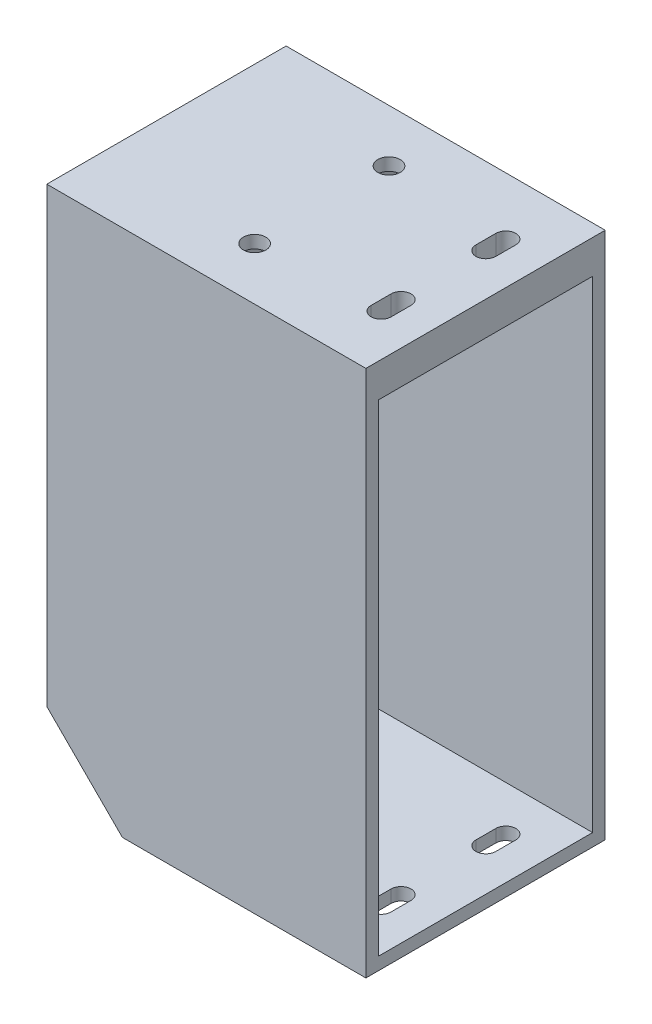
SolidWorks part; units mm, degrees
ref_plane "Front Plane" through (0, 0, 0) normal (0, 0, 1) x (1, 0, 0)
ref_plane "Top Plane" through (0, 0, 0) normal (0, 1, 0) x (1, 0, 0)
ref_plane "Right Plane" through (0, 0, 0) normal (1, 0, 0) x (0, 0, -1)
sketch "Sketch2" plane through (0, 0, 0) normal (1, 0, 0) x (0, 0, -1)
  line L0 (-22.6038, 17.8808) -> (-22.6038, -96.8692)
  line L1 (-22.6038, -96.8692) -> (28.3962, -96.8692)
  line L2 (28.3962, -96.8692) -> (28.3962, 17.8808)
  line L3 (28.3962, 17.8808) -> (-22.6038, 17.8808)
  line L4 (-25.6038, 20.8808) -> (-25.6038, -99.8692)
  line L5 (-25.6038, -99.8692) -> (31.3962, -99.8692)
  line L6 (31.3962, -99.8692) -> (31.3962, 20.8808)
  line L7 (31.3962, 20.8808) -> (-25.6038, 20.8808)
  dimension "D1" = 51
  dimension "D2" = 114.75
  dimension "D3" = 3
extrude "Boss-Extrude1" add sketch "Sketch2" along normal blind 75
sketch "Sketch3" plane through (0, 0, 0) normal (-1, 0, 0) x (0, 0, 1)
  line L0 (-31.3962, 20.8808) -> (25.6038, 20.8808)
  line L1 (25.6038, 20.8808) -> (25.6038, -99.8692)
  line L2 (25.6038, -99.8692) -> (-31.3962, -99.8692)
  line L3 (-31.3962, -99.8692) -> (-31.3962, 20.8808)
extrude "Boss-Extrude2" add sketch "Sketch3" along normal blind 3
sketch "Sketch4" plane through (0, 20.8808, 0) normal (0, 1, 0) x (1, 0, 0)
  line L0 (-3, 31.3962) -> (75, 31.3962)
  line L1 (75, 31.3962) -> (75, -25.6038)
  line L2 (75, -25.6038) -> (-3, -25.6038)
  line L3 (-3, -25.6038) -> (-3, 31.3962)
extrude "Boss-Extrude3" add sketch "Sketch4" along normal blind 5
sketch "Sketch6" plane through (0, 25.8808, 0) normal (0, 1, 0) x (1, 0, 0)
  line L0 (36, 31.3962) -> (36, -25.6038) construction
  line L1 (75, 31.3962) -> (-3, 31.3962) construction
  line L2 (-3, -25.6038) -> (75, -25.6038) construction
  line L3 (-3, 2.8962) -> (75, 2.8962) construction
  line L4 (-3, 31.3962) -> (-3, -25.6038) construction
  line L5 (75, -25.6038) -> (75, 31.3962) construction
  circle A0 centre (36, 18.8962) radius 2.675
  circle A1 centre (36, -13.1038) radius 2.675
  dimension "D1" = 5.35
  dimension "D2" = 12.5
extrude "Cut-Extrude2" cut sketch "Sketch6" against normal blind 10
sketch "Sketch8" plane through (0, 0, -31.3962) normal (0, 0, -1) x (-1, 0, 0)
  line L0 (3, -99.8692) -> (3, -79.8692)
  line L1 (3, 25.8808) -> (3, -99.8692) construction
  line L2 (3, -79.8692) -> (-17, -99.8692)
  line L3 (-75, -99.8692) -> (3, -99.8692) construction
  line L4 (-17, -99.8692) -> (3, -99.8692)
  dimension "D1" = 20
  dimension "D2" = 20
extrude "Cut-Extrude3" cut sketch "Sketch8" against normal through all
sketch "Sketch9" plane through (0, 0, 25.6038) normal (0, 0, 1) x (1, 0, 0)
  line L0 (-3, -79.8692) -> (17, -99.8692)
  line L1 (17, -99.8692) -> (21.2426, -99.8692)
  line L3 (-3, -79.8692) -> (-3, -75.6266)
  line L5 (0, -78.6266) -> (18.2426, -96.8692) construction
  line L6 (-3, -75.6266) -> (21.2426, -99.8692)
  line L8 (0, -78.6266) -> (0, -70.8578) construction
  line L9 (18.2426, -96.8692) -> (26.9937, -96.8692) construction
  line L10 (-3, -79.8692) -> (-3, -70.8578) construction
  line L11 (17, -99.8692) -> (26.9937, -99.8692) construction
  dimension "D1" = 3
extrude "Boss-Extrude4" add sketch "Sketch9" against normal up to next
sketch "Sketch15" plane through (0, -99.8692, 0) normal (0, -1, 0) x (1, 0, 0)
  line L0 (65, 9.6038) -> (65, -15.3962) construction
  line L1 (62.625, 7.2263) -> (62.625, 11.9763)
  line L2 (67.375, 7.2263) -> (67.375, 11.9763)
  line L3 (62.625, -17.7276) -> (62.625, -12.9776)
  line L4 (67.375, -17.7276) -> (67.375, -12.9776)
  line L5 (75, 25.6038) -> (75, -31.3962) construction
  arc A0 (62.625, -17.7276) -> (67.375, -17.7276) centre (65, -17.7276) ccw
  arc A2 (62.625, 7.2263) -> (67.375, 7.2263) centre (65, 7.2263) ccw
  arc A3 (67.375, 11.9763) -> (62.625, 11.9763) centre (65, 11.9763) ccw
  arc A4 (67.375, -12.9776) -> (62.625, -12.9776) centre (65, -12.9776) ccw
  dimension "D1" = 2.375
  dimension "D2" = 25
  dimension "D3" = 10
  dimension "D4" = 16
  dimension "D5" = 4.75
extrude "Cut-Extrude7" cut sketch "Sketch15" against normal through all
sketch "Sketch18" plane through (-3, 0, 0) normal (-1, 0, 0) x (0, 0, 1)
  line L0 (-2.8962, 30.7558) -> (-2.8962, -84.7442) construction
  line L1 (11.3538, 13.3808) -> (11.3538, -41.6192)
  line L2 (-17.1462, 13.3808) -> (-17.1462, -41.6192)
  line L3 (-31.3962, -14.1192) -> (25.6038, -14.1192) construction
  line L4 (-17.1462, -41.6192) -> (11.3538, -41.6192)
  line L5 (-17.1462, 13.3808) -> (11.3538, 13.3808)
  line L6 (11.3538, -14.1192) -> (-17.1462, -14.1192) construction
  circle A0 centre (-22.8962, -14.1192) radius 1.75
  circle A1 centre (17.1038, -14.1192) radius 1.75
  dimension "D2" = 3.5
  dimension "D1" = 40
  dimension "D3" = 40
  dimension "D4" = 55
extrude "Cut-Extrude8" cut sketch "Sketch18" against normal blind 10
sketch "Sketch21" plane through (0, 0, 0) normal (1, 0, 0) x (0, 0, -1)
  line L0 (-25.6038, 25.8808) -> (31.3962, 25.8808) construction
  line L1 (-15.415, -11.1942) -> (-18.7925, -11.1942)
  line L2 (-18.7925, -11.1942) -> (-20.4813, -14.1192)
  line L3 (-20.4813, -14.1192) -> (-18.7925, -17.0442)
  line L4 (-18.7925, -17.0442) -> (-15.415, -17.0442)
  line L5 (-15.415, -17.0442) -> (-13.7263, -14.1192)
  line L6 (-13.7263, -14.1192) -> (-15.415, -11.1942)
  line L7 (2.8962, -78.6266) -> (2.8962, 17.8808) construction
  line L8 (28.3962, -78.6266) -> (-22.6038, -78.6266) construction
  line L9 (28.3962, 17.8808) -> (-22.6038, 17.8808) construction
  line L10 (19.5187, -14.1192) -> (21.2075, -11.1942)
  line L11 (21.2075, -17.0442) -> (19.5187, -14.1192)
  line L12 (24.585, -17.0442) -> (21.2075, -17.0442)
  line L13 (26.2737, -14.1192) -> (24.585, -17.0442)
  line L14 (24.585, -11.1942) -> (26.2737, -14.1192)
  line L15 (21.2075, -11.1942) -> (24.585, -11.1942)
  line L16 (22.8962, -19.8692) -> (28.6462, -19.8692)
  line L17 (28.6462, -19.8692) -> (28.6462, -8.3692)
  line L18 (28.6462, -8.3692) -> (22.8962, -8.3692)
  line L19 (-17.1038, -19.8692) -> (-22.8538, -19.8692)
  line L20 (-22.8538, -8.3692) -> (-17.1038, -8.3692)
  line L21 (-22.8538, -19.8692) -> (-22.8538, -8.3692)
  circle A0 centre (-17.1038, -14.1192) radius 2.925 construction
  circle A1 centre (22.8962, -14.1192) radius 2.925 construction
  arc A2 (22.8962, -8.3692) -> (22.8962, -19.8692) centre (22.8962, -14.1192) ccw
  arc A3 (-17.1038, -8.3692) -> (-17.1038, -19.8692) centre (-17.1038, -14.1192) cw
  dimension "D1" = 5.85
extrude "Boss-Extrude6" add sketch "Sketch21" along normal blind 5
sketch "Sketch22" plane through (0, 17.8808, 0) normal (0, -1, 0) x (1, 0, 0)
  line L0 (0, -2.8962) -> (75, -2.8962) construction
  line L1 (0, -28.3962) -> (0, 22.6038) construction
  line L2 (75, -28.3962) -> (75, 22.6038) construction
  line L3 (75, -28.3962) -> (0, -28.3962) construction
  line L4 (40.8209, -18.8962) -> (38.4104, -14.7212)
  line L5 (38.4104, -14.7212) -> (33.5896, -14.7212)
  line L6 (33.5896, -14.7212) -> (31.1791, -18.8962)
  line L7 (31.1791, -18.8962) -> (33.5896, -23.0712)
  line L8 (33.5896, -23.0712) -> (38.4104, -23.0712)
  line L9 (38.4104, -23.0712) -> (40.8209, -18.8962)
  line L10 (38.4104, 17.2788) -> (40.8209, 13.1038)
  line L11 (33.5896, 17.2788) -> (38.4104, 17.2788)
  line L12 (31.1791, 13.1038) -> (33.5896, 17.2788)
  line L13 (33.5896, 8.9288) -> (31.1791, 13.1038)
  line L14 (38.4104, 8.9288) -> (33.5896, 8.9288)
  line L15 (40.8209, 13.1038) -> (38.4104, 8.9288)
  circle A0 centre (36, -18.8962) radius 4.175 construction
  circle A1 centre (36, 13.1038) radius 4.175 construction
  dimension "D1" = 8.35
extrude "Cut-Extrude9" cut sketch "Sketch22" against normal blind 5
chamfer "Chamfer1" distance 2 angle 45 3 edges at (-3, -26.9942, 25.6038) (-3, 25.8808, -2.8962) (-3, -26.9942, -31.3962)
